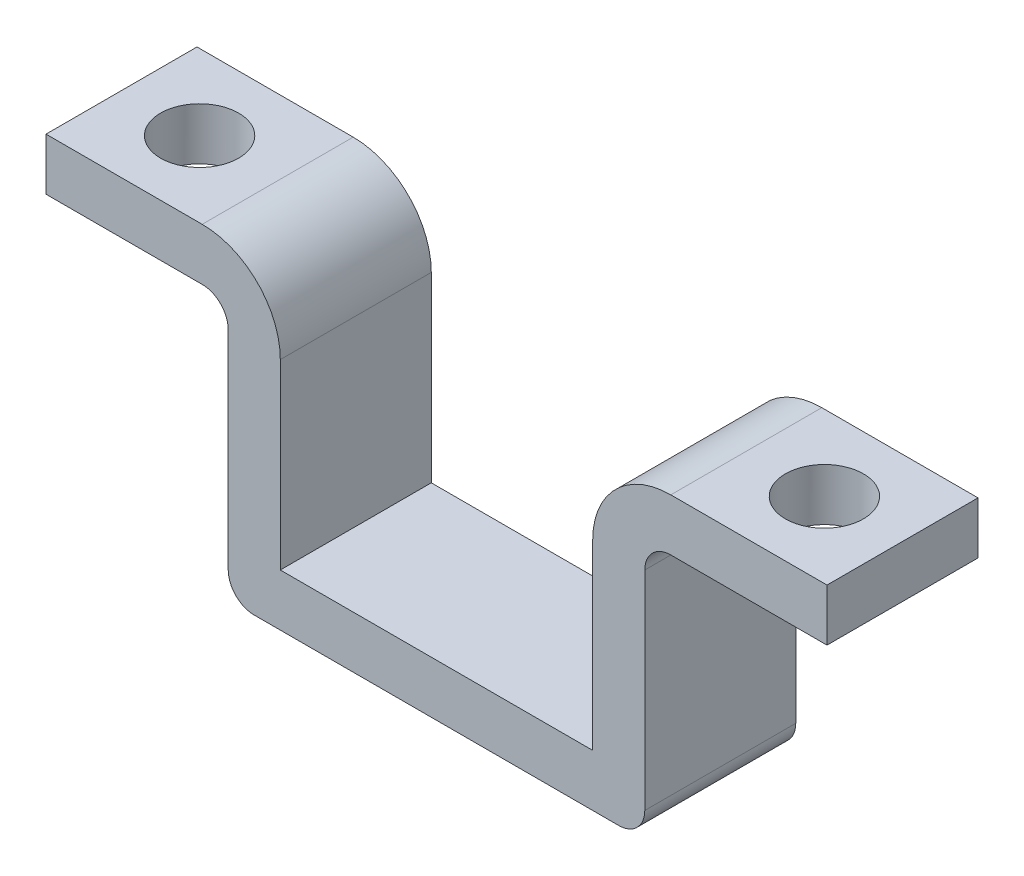
SolidWorks part; units mm, degrees
ref_plane "Front Plane" through (0, 0, 0) normal (0, 0, 1) x (1, 0, 0)
ref_plane "Top Plane" through (0, 0, 0) normal (0, 1, 0) x (1, 0, 0)
ref_plane "Right Plane" through (0, 0, 0) normal (1, 0, 0) x (0, 0, -1)
sketch "Sketch2" plane through (0, 0, 0) normal (0, 0, 1) x (1, 0, 0)
  line L1 (-5, 5) -> (5, 5)
  line L2 (-6, 4) -> (-6, -4)
  line L3 (-5, -5) -> (5, -5)
  line L4 (6, 4) -> (6, -4)
  arc A0 (-6, -4) -> (-5, -5) centre (-5, -4) ccw
  arc A1 (5, -5) -> (6, -4) centre (5, -4) ccw
  arc A2 (6, 4) -> (5, 5) centre (5, 4) ccw
  arc A3 (-6, 4) -> (-5, 5) centre (-5, 4) cw
  circle A4 centre (-4.5, 0) radius 0.8
  circle A5 centre (4.5, 0) radius 0.8
  circle A6 centre (0, 0) radius 2
  point P4 (0, 5)
  point P6 (6, 0)
  dimension "D1" = 1
  dimension "D6" = 1.6
  dimension "D7" = 4
  dimension "D2" = 12
  dimension "D3" = 10
  dimension "D4" = 4.5
  dimension "D5" = 4.5
sketch "Sketch3" plane through (0, 0, 0) normal (0, 0, 1) x (1, 0, 0)
  line L0 (-6, -5) -> (6, -5)
  line L1 (6, -5) -> (6, 2)
  line L2 (-6, -5) -> (-6, 2)
  line L3 (-5, -5) -> (5, -5) construction
  line L4 (-6, 4) -> (-6, -4) construction
  line L5 (8, -6) -> (8, 2)
  line L6 (-7, -7) -> (7, -7)
  line L7 (-8, -6) -> (-8, 2)
  line L8 (-8, -7) -> (-8, 5.1614) construction
  line L9 (-9, 3) -> (-15, 3)
  line L10 (-15, 3) -> (-15, 5)
  line L11 (-15, 5) -> (-9, 5)
  line L12 (-6, -5) -> (-6, 5.1614) construction
  line L13 (-5, 5) -> (5, 5) construction
  line L14 (8, -7) -> (8, 5.1614) construction
  line L15 (9, 5) -> (15, 5)
  line L16 (15, 5) -> (15, 3)
  line L17 (15, 3) -> (9, 3)
  line L18 (6, -5) -> (6, 5.1614) construction
  line L19 (-8, -7) -> (8, -7) construction
  arc A0 (-8, 2) -> (-9, 3) centre (-9, 2) ccw
  arc A1 (-6, 2) -> (-9, 5) centre (-9, 2) ccw
  arc A2 (9, 3) -> (8, 2) centre (9, 2) ccw
  arc A3 (9, 5) -> (6, 2) centre (9, 2) ccw
  arc A4 (-7, -7) -> (-8, -6) centre (-7, -6) cw
  arc A5 (8, -6) -> (7, -7) centre (7, -6) cw
  point P6 (0, -5)
  point P7 (0, -5)
  dimension "D3" = 1
  dimension "D4" = 3
  dimension "D6" = 1
  dimension "D7" = 3
  dimension "D10" = 1
  dimension "D11" = 1
  dimension "D2" = 2
  dimension "D5" = 6
  dimension "D8" = 2
  dimension "D9" = 6
  dimension "D1" = 2
extrude "Boss-Extrude1" add sketch "Sketch3" along normal mid plane 5.8
sketch "Sketch5" plane through (0, 5, 0) normal (0, 1, 0) x (1, 0, 0)
  line L0 (-9, 2.9) -> (-15, 2.9) construction
  line L1 (15, 2.9) -> (9, 2.9) construction
  circle A0 centre (12, 0) radius 1.5
  circle A1 centre (-12, 0) radius 1.5
  point P4 (0, 0)
  point P6 (0, 0)
  point P9 (-12, 2.9)
  point P12 (12, 2.9)
  dimension "D1" = 3
  dimension "D2" = 3
extrude "Cut-Extrude1" cut sketch "Sketch5" against normal through all
equation "\"D9@Sketch3\"=\"D5@Sketch3\""
